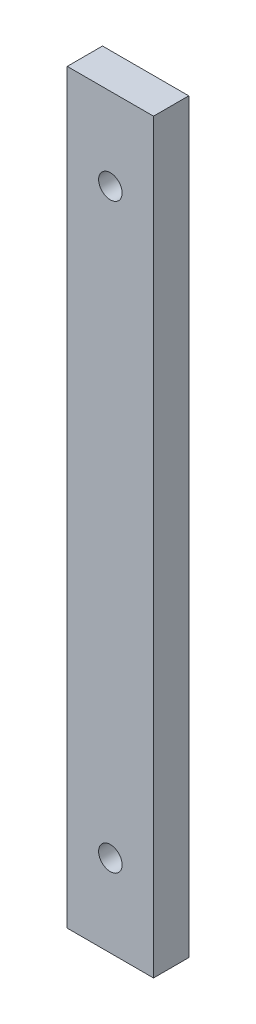
SolidWorks part; units mm, degrees
material "Acrylic (Medium-high impact)"
ref_plane "Front Plane" through (0, 0, 0) normal (0, 0, 1) x (1, 0, 0)
ref_plane "Top Plane" through (0, 0, 0) normal (0, 1, 0) x (1, 0, 0)
ref_plane "Right Plane" through (0, 0, 0) normal (1, 0, 0) x (0, 0, -1)
sketch "Sketch1" plane through (0, 0, 0) normal (0, 0, 1) x (1, 0, 0)
  line L1 (-7.34, 63.5) -> (7.34, 63.5)
  line L2 (-7.34, 63.5) -> (-7.34, -63.5)
  line L3 (-7.34, -63.5) -> (7.34, -63.5)
  line L4 (7.34, 63.5) -> (7.34, -63.5)
  line L5 (-7.34, 63.5) -> (7.34, -63.5) construction
  line L6 (-7.34, -63.5) -> (7.34, 63.5) construction
  point P0 (0, 0)
  dimension "D1" = 14.68
  dimension "D2" = 127
extrude "Boss-Extrude1" add sketch "Sketch1" along normal blind 6
sketch "Sketch2" plane through (0, 0, 6) normal (0, 0, 1) x (1, 0, 0)
  line L0 (0, -63.5) -> (0, -49.5)
  line L1 (-7.34, 63.5) -> (7.34, 63.5)
  line L2 (-7.34, 63.5) -> (-7.34, -63.5)
  line L3 (-7.34, -63.5) -> (7.34, -63.5)
  line L4 (7.34, 63.5) -> (7.34, -63.5)
  line L5 (-7.34, 0) -> (7.34, 0)
  circle A0 centre (0, -49.5) radius 2
  circle A1 centre (0, 49.5) radius 2
extrude "Cut-Extrude1" cut sketch "Sketch2" against normal blind 6
